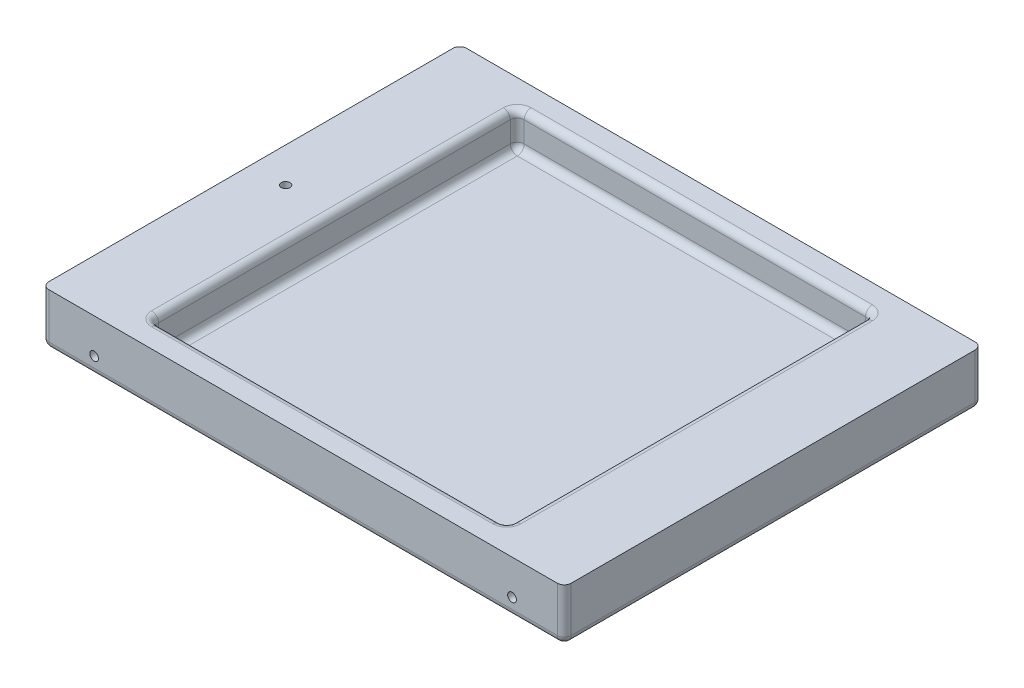
SolidWorks part; units mm, degrees
ref_plane "Front Plane" through (0, 0, 0) normal (0, 0, 1) x (1, 0, 0)
ref_plane "Top Plane" through (0, 0, 0) normal (0, 1, 0) x (1, 0, 0)
ref_plane "Right Plane" through (0, 0, 0) normal (1, 0, 0) x (0, 0, -1)
sketch "Sketch2" plane through (0, 0, 0) normal (0, 0, 1) x (1, 0, 0)
  line L1 (-750, 75) -> (750, 75)
  line L2 (-750, 75) -> (-750, -75)
  line L3 (-750, -75) -> (750, -75)
  line L4 (750, 75) -> (750, -75)
  line L5 (-750, 75) -> (750, -75) construction
  line L6 (-750, -75) -> (750, 75) construction
  point P0 (0, 0)
  dimension "D1" = 150
  dimension "D2" = 1500
extrude "Boss-Extrude1" add sketch "Sketch2" along normal mid plane 1200
sketch "Sketch3" plane through (0, 0, 600) normal (0, 0, 1) x (1, 0, 0)
  line L0 (-750, -75) -> (750, -75) construction
  line L1 (-750, 75) -> (-750, -75) construction
  circle A0 centre (-600, -25) radius 12.5
  dimension "D1" = 25
  dimension "D2" = 50
  dimension "D3" = 150
extrude "Cut-Extrude2" cut sketch "Sketch3" against normal blind 250
mirror "Mirror2" about plane through (0, 0, 0) normal (1, 0, 0) of "Cut-Extrude2"
mirror "Mirror3" about plane through (0, 0, 0) normal (0, 0, 1) of "Mirror2", "Cut-Extrude2"
sketch "Sketch4" plane through (0, 75, 0) normal (0, 1, 0) x (1, 0, 0)
  line L0 (-750, -600) -> (-750, 600) construction
  circle A0 centre (-650, 0) radius 12.5
  point P2 (0, 0)
  dimension "D1" = 25
  dimension "D2" = 100
extrude "Cut-Extrude3" cut sketch "Sketch4" against normal blind 50 contours A0
sketch "Sketch5" plane through (0, 75, 0) normal (0, 1, 0) x (1, 0, 0)
  line L1 (-510, 525) -> (510, 525)
  line L2 (-510, 525) -> (-510, -525)
  line L3 (-510, -525) -> (510, -525)
  line L4 (510, 525) -> (510, -525)
  line L5 (-510, 525) -> (510, -525) construction
  line L6 (-510, -525) -> (510, 525) construction
  point P1 (0, 0)
  dimension "D1" = 1050
  dimension "D2" = 1020
extrude "Cut-Extrude4" cut sketch "Sketch5" against normal blind 100
fillet "Fillet1" radius 20 20 edges at (510, 25, -525) (0, -25, -525) (510, -25, 0) (510, 75, 0) (0, 75, -525) (-510, 25, -525) (-510, -25, 0) (-510, 75, 0) (-510, 25, 525) (0, -25, 525) (510, 25, 525) (0, 75, 525) (750, -75, 0) (750, 0, 600) (0, -75, 600) (-750, 0, 600) (-750, -75, 0) (-750, 0, -600) (0, -75, -600) (750, 0, -600)
